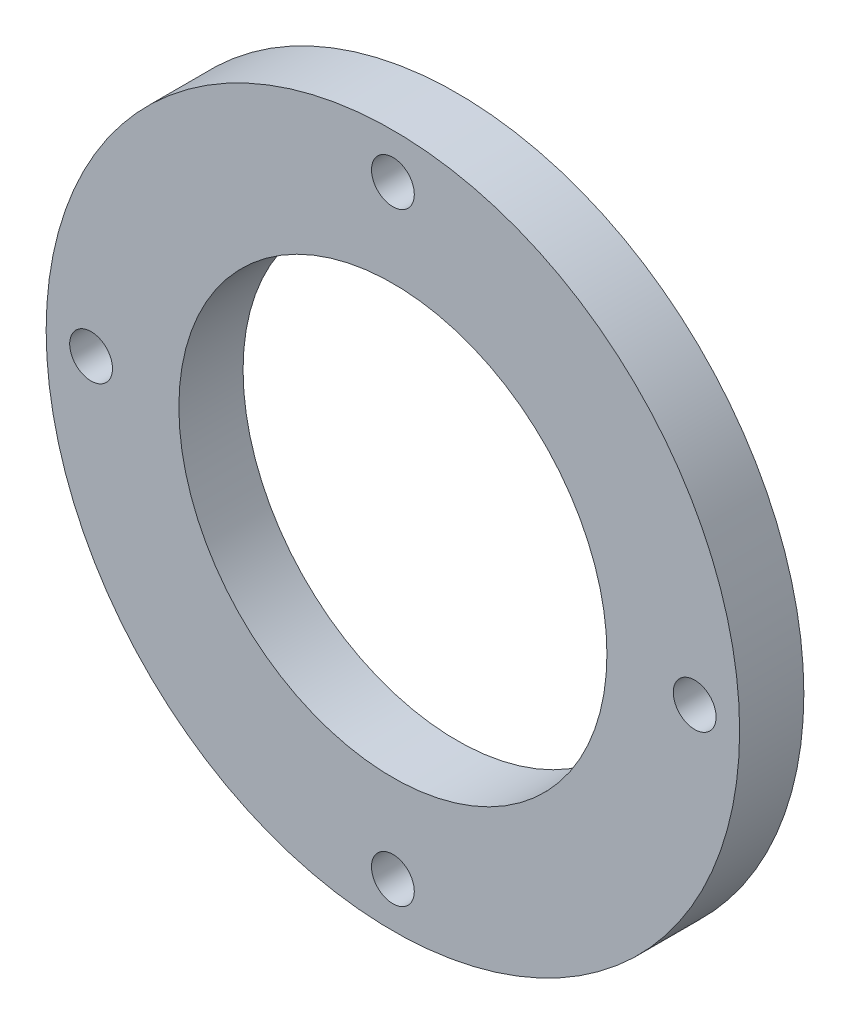
SolidWorks part; units mm, degrees
ref_plane "Alzado" through (0, 0, 0) normal (0, 0, 1) x (1, 0, 0)
ref_plane "Planta" through (0, 0, 0) normal (0, 1, 0) x (1, 0, 0)
ref_plane "Vista lateral" through (0, 0, 0) normal (1, 0, 0) x (0, 0, -1)
sketch "Croquis1" plane through (0, 0, 0) normal (0, 0, 1) x (1, 0, 0)
  circle A0 centre (0, 0) radius 81
  circle A1 centre (0, 0) radius 50
  dimension "D1" = 162
  dimension "D2" = 100
extrude "Saliente-Extruir1" add sketch "Croquis1" along normal blind 15
sketch "Croquis2" plane through (0, 0, 15) normal (0, 0, 1) x (1, 0, 0)
  line L1 (-7.5, 81) -> (7.5, 81)
  line L2 (-7.5, 81) -> (-7.5, -81)
  line L3 (-7.5, -81) -> (7.5, -81)
  line L4 (7.5, 81) -> (7.5, -81)
  line L5 (-7.5, 81) -> (7.5, -81) construction
  line L6 (-7.5, -81) -> (7.5, 81) construction
  line L7 (-81, 7.5) -> (81, 7.5)
  line L8 (-81, 7.5) -> (-81, -7.5)
  line L9 (-81, -7.5) -> (81, -7.5)
  line L10 (81, 7.5) -> (81, -7.5)
  line L11 (-81, 7.5) -> (81, -7.5) construction
  line L12 (-81, -7.5) -> (81, 7.5) construction
  circle A1 centre (0, 70.5) radius 5
  circle A2 centre (-70.5, 0) radius 5
  circle A3 centre (0, -70.5) radius 5
  circle A4 centre (70.5, 0) radius 5
  point P0 (0, 0)
  point P6 (0, 0)
  point P13 (0, 0)
  point P18 (0, 0)
  dimension "D5" = 10
  dimension "D7" = 10
  dimension "D9" = 10
  dimension "D11" = 10
  dimension "D1" = 162
  dimension "D2" = 15
  dimension "D3" = 162
  dimension "D4" = 15
  dimension "D6" = 10.5
  dimension "D8" = 10.5
  dimension "D10" = 10.5
  dimension "D12" = 10.5
extrude "Cortar-Extruir1" cut sketch "Croquis2" against normal up to surface (15 mm away) contours A1 | A2 | A4 | A3 up to face at (81, 0, 0)
